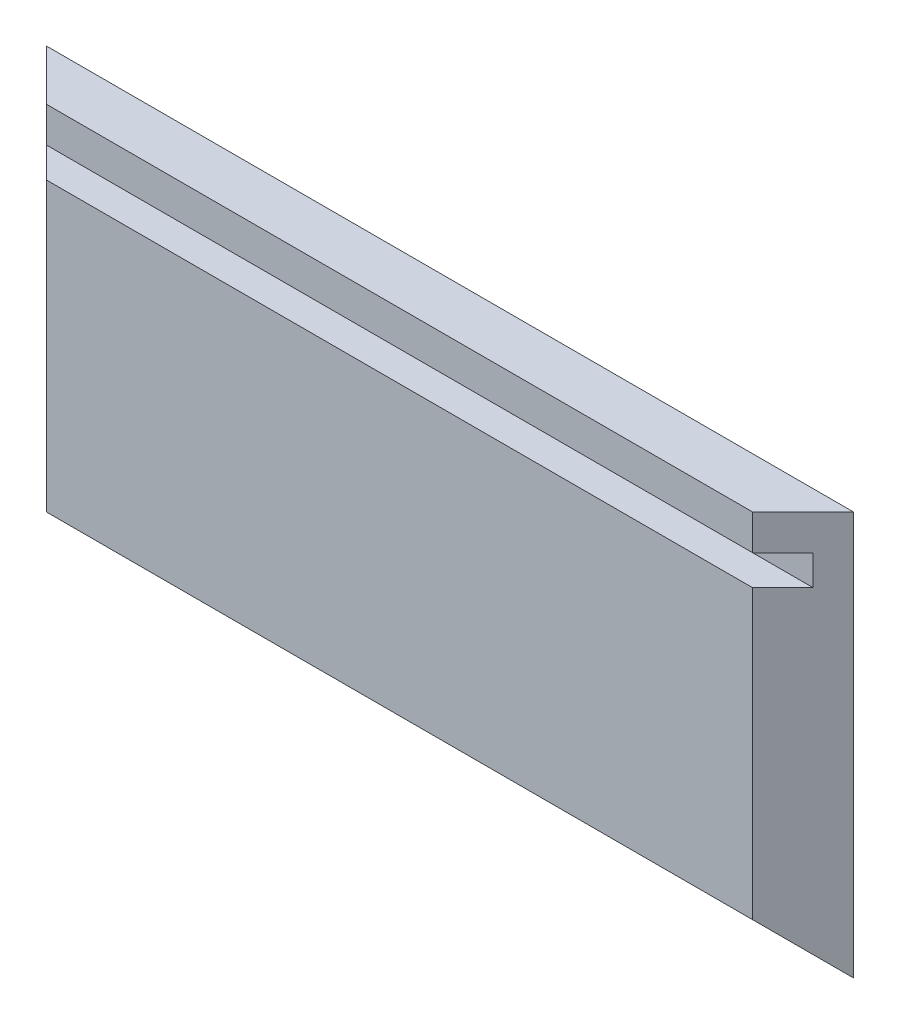
SolidWorks part; units mm, degrees
ref_plane "Front Plane" through (0, 0, 0) normal (0, 0, 1) x (1, 0, 0)
ref_plane "Top Plane" through (0, 0, 0) normal (0, 1, 0) x (1, 0, 0)
ref_plane "Right Plane" through (0, 0, 0) normal (1, 0, 0) x (0, 0, -1)
sketch "Sketch3" plane through (0, 0, 0) normal (0, 1, 0) x (1, 0, 0)
  line L0 (-40, 2.5) -> (-35, -2.5)
  line L1 (-40, 2.5) -> (40, 2.5)
  line L2 (-40, 2.5) -> (-40, -2.5) construction
  line L3 (-35, -2.5) -> (35, -2.5)
  line L4 (40, 2.5) -> (40, -2.5) construction
  line L5 (-40, 2.5) -> (40, -2.5) construction
  line L6 (-40, -2.5) -> (40, 2.5) construction
  line L7 (40, 2.5) -> (35, -2.5)
  point P0 (0, 0)
  dimension "D1" = 5
  dimension "D2" = 80
  dimension "D3" = 45
  dimension "D4" = 45
extrude "Boss-Extrude2" add sketch "Sketch3" along normal blind 40
sketch "Sketch4" plane through (0, 0, 0) normal (1, 0, 0) x (0, 0, -1)
  line L0 (-2.5, 0) -> (2.5, 0) construction
  line L1 (-2.5, 0) -> (2.5, 0)
  line L2 (2.5, 0) -> (-2.5, 5)
  line L3 (-2.5, 40) -> (-2.5, 0) construction
  line L4 (-2.5, 5) -> (-2.5, 0)
  dimension "D1" = 45
extrude "Cut-Extrude1" cut sketch "Sketch4" against normal through all both and the other way through all
sketch "Sketch7" plane through (0, 0, 0) normal (1, 0, 0) x (0, 0, -1)
  line L0 (2.5, 40) -> (2.5, 0) construction
  line L2 (-2.5, 36.5) -> (-2.5, 33.5) construction
  line L4 (2.5, 40) -> (2.5, 30) construction
  line L5 (-2.5, 35) -> (2.5, 35) construction
  line L6 (-2.5, 36.5) -> (0.5, 36.5)
  line L7 (-2.5, 33.5) -> (0.5, 33.5)
  line L8 (0.5, 36.5) -> (0.5, 33.5)
  line L9 (-2.5, 36.5) -> (-2.5, 33.5)
  dimension "D1" = 10
  dimension "D2" = 1.5
  dimension "D3" = 3
extrude "Cut-Extrude2" cut sketch "Sketch7" against normal through all both and the other way through all
